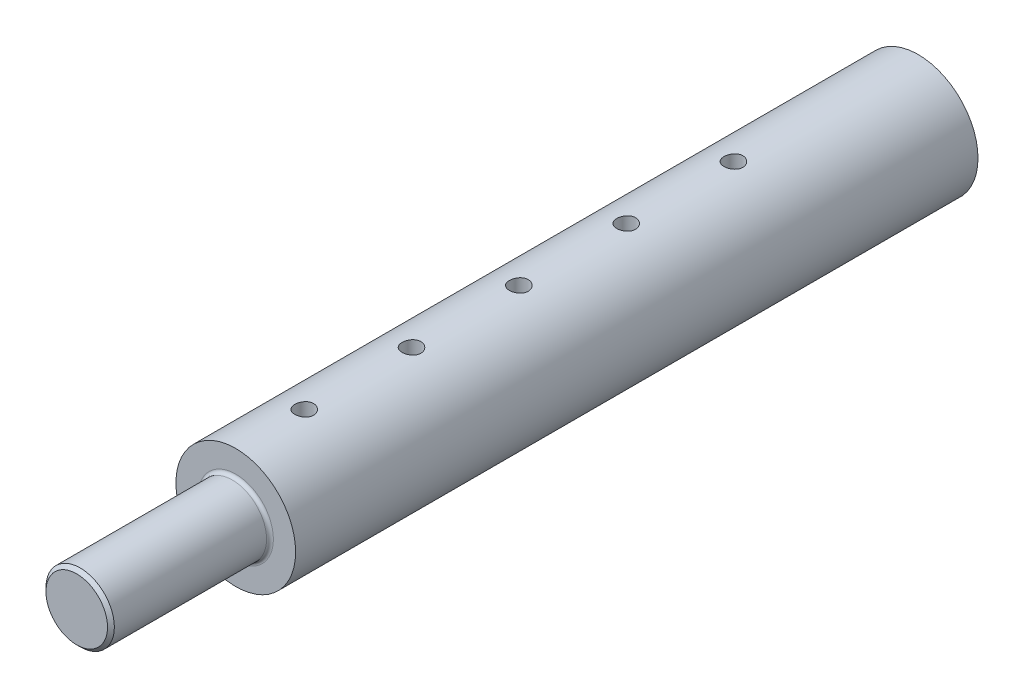
SolidWorks part; units mm, degrees
material "Acier allié inoxydable"
ref_plane "Plan de face" through (0, 0, 0) normal (0, 0, 1) x (1, 0, 0)
ref_plane "Plan de dessus" through (0, 0, 0) normal (0, 1, 0) x (1, 0, 0)
ref_plane "Plan de droite" through (0, 0, 0) normal (1, 0, 0) x (0, 0, -1)
sketch "Esquisse1" plane through (0, 0, 0) normal (0, 0, 1) x (1, 0, 0)
  circle A1 centre (0, 0) radius 17.5
  dimension "D1" = 35
extrude "Boss.-Extru.1" add sketch "Esquisse1" along normal blind 246
sketch "Esquisse2" plane through (0, 0, 0) normal (0, 0, -1) x (-1, 0, 0)
  circle A0 centre (0, 0) radius 12
  dimension "D1" = 24
extrude "Enlèv. mat.-Extru.1" cut sketch "Esquisse2" against normal blind 44
ref_plane "Plan1" through (0, 0, 44) normal (0, 0, -1) x (-1, 0, 0)
sketch "Esquisse3" plane through (0, 0, 246) normal (0, 0, 1) x (1, 0, 0)
  circle A0 centre (0, 0) radius 7
  dimension "D1" = 14
extrude "Enlèv. mat.-Extru.2" [suppressed] cut sketch "Esquisse3" against normal up to surface (120 mm away)
hole_wizard "Dégagement M61" positions "Esquisse5" profile "Esquisse4" hole size "M6" standard "ISO"
sketch "Esquisse5" plane through (0, 0, 30) normal (0, 0, -1) x (-1, 0, 0)
  point P0 (0, 0)
sketch "Esquisse4" plane through (0, 0, 30) normal (1, 0, 0) x (0, 1, 0)
  line L0 (0, 0) -> (0, 18.103)
  line L1 (0, 18.103) -> (3.5, 16)
  line L2 (3.5, 16) -> (3.5, 0)
  line L5 (3.5, 0) -> (0, 0)
  line L10 (0, 18.103) -> (-3.5, 16) construction
  line L11 (0, -6.35) -> (0, 107.95) construction
  dimension "Diamètre du perçage" = 7
  dimension "Profondeur du perçage" = 16
  dimension "Angle de pointe" = 118
ref_plane "Plan2" through (0, 17.5, 0) normal (0, 1, 0) x (1, 0, 0)
hole_wizard "Trou taraudé M61" positions "Esquisse8" profile "Esquisse7" tap size "M6" standard "ISO"
sketch "Esquisse8" plane through (0, 15, 0) normal (0, 1, 0) x (1, 0, 0)
  line L0 (-15, -34) -> (15, -34) construction
  line L1 (-15, 0) -> (-15, -176) construction
  line L2 (15, -176) -> (15, 0) construction
  line L4 (15, 0) -> (-15, 0) construction
  line L5 (0, -15) -> (0, -34) construction
  point P0 (0, -22)
  point P2 (0, -29)
  point P14 (0, -15)
  dimension "D1" = 34
  dimension "D2" = 5
  dimension "D3" = 7
  dimension "D4" = 7
sketch "Esquisse7" plane through (0, 15, 22) normal (1, 0, 0) x (0, 0, 1)
  line L0 (0, 0) -> (0, 5.5)
  line L1 (0, 5.5) -> (2.5, 5.5)
  line L2 (2.5, 5.5) -> (2.5, 0)
  line L5 (2.5, 0) -> (0, 0)
  line L11 (0, -6.35) -> (0, 107.95) construction
  dimension "Diamètre du trou pour taraudage jusqu'au prochain" = 5
  dimension "Profondeur du trou pour taraudage jusqu'au prochain" = 5.5
cosmetic thread "Filetage de perçage1" [suppressed] parameters "D2"=6
cosmetic thread "Filetage de perçage2" [suppressed] parameters "D2"=6
cosmetic thread "Filetage de perçage3" [suppressed] parameters "D2"=6
hole_wizard "Trou taraudé M62" positions "Esquisse3D1" profile "Esquisse12" tap size "M6" standard "ISO"
sketch3d "Esquisse3D1"
  line L0 (-17.5, 0, 18) -> (-17.5, 0, 32) construction
  point P0 (-17.5, 0, 32)
  point P2 (-17.5, 0, 25)
  point P4 (-17.5, 0, 18)
  point P33 (-17.5, 0, 25)
  point P35 (-17.5, 0, 25)
  point P39 (-17.5, 0, 25)
  point P42 (-17.5, 0, 25)
  dimension "D1" = 7
  dimension "D2" = 12
sketch "Esquisse12" plane through (-17.5, 0, 32) normal (0, 1, 0) x (0, 0, 1)
  line L0 (0, 0) -> (0, 5.5)
  line L1 (0, 5.5) -> (2.5, 5.5)
  line L2 (2.5, 5.5) -> (2.5, 0)
  line L5 (2.5, 0) -> (0, 0)
  line L11 (0, -6.35) -> (0, 107.95) construction
  dimension "Diamètre du trou pour taraudage jusqu'au prochain" = 5
  dimension "Profondeur du trou pour taraudage jusqu'au prochain" = 5.5
cosmetic thread "Filetage de perçage4" parameters "D2"=6
cosmetic thread "Filetage de perçage8" parameters "D2"=6
cosmetic thread "Filetage de perçage9" parameters "D2"=6
cosmetic thread "Filetage de perçage10" parameters "D2"=6
sketch "Esquisse11" plane through (0, 0, 246) normal (0, 0, 1) x (1, 0, 0)
  circle A0 centre (0, 0) radius 10
  circle A1 centre (0, 0) radius 17.5 construction
  circle M2 centre (0, 0) radius 17.5
  dimension "D1" = 20
extrude "Enlèv. mat.-Extru.3" cut sketch "Esquisse11" against normal offset from surface (46.5 mm away) 199.5 contours A0 M2 up to face at (-12, 0, 0)
fillet "Congé1" radius 1 1 edges at (10, 0, 199.5)
chamfer "Chanfrein1" distance 1 angle 45 2 edges at (10, 0, 246) (-12, 0, 0)
hole_wizard "Trou pour taraudage pour trou taraudé M62" positions "Esquisse10" profile "Esquisse9" hole size "M6" standard "ISO" end condition through all
sketch "Esquisse10" plane through (0, 17.5, 0) normal (0, 1, 0) x (1, 0, 0)
  line L0 (0, -54) -> (0, -116.75) construction
  line L1 (0, -116.75) -> (0, -179.5) construction
  line L10 (13.2, -44) -> (-13.2, -44) construction
  line L11 (0, -54) -> (0, -44)
  line L16 (-17.5, -199.5) -> (17.5, -199.5) construction
  point P0 (0, -54)
  point P2 (0, -116.75)
  point P4 (0, -179.5)
  point P40 (0, -85.375)
  point P42 (0, -148.125)
  dimension "D1" = 20
  dimension "D2" = 10
sketch "Esquisse9" plane through (0, 17.5, 54) normal (1, 0, 0) x (0, 0, 1)
  line L0 (0, 0) -> (0, 35)
  line L1 (0, 35) -> (2.75, 35)
  line L2 (2.75, 35) -> (2.75, 0)
  line L5 (2.75, 0) -> (0, 0)
  line L11 (0, -6.35) -> (0, 107.95) construction
  dimension "Diamètre du perçage jusqu'au prochain" = 5.5
  dimension "Profondeur du perçage jusqu'au prochain" = 35
